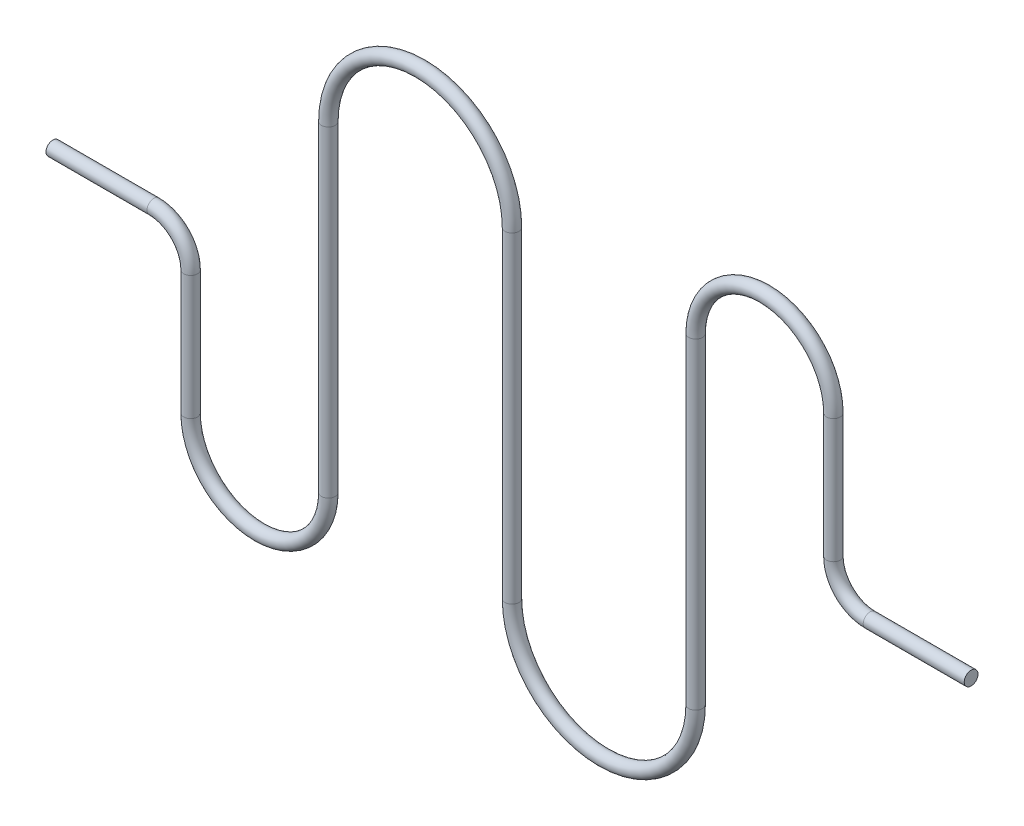
SolidWorks part; units mm, degrees
material "1060 Alloy"
ref_plane "Front Plane" through (0, 0, 0) normal (0, 0, 1) x (1, 0, 0)
ref_plane "Top Plane" through (0, 0, 0) normal (0, 1, 0) x (1, 0, 0)
ref_plane "Right Plane" through (0, 0, 0) normal (1, 0, 0) x (0, 0, -1)
sketch "Sketch4" plane through (0, 0, 0) normal (0, 0, 1) x (1, 0, 0)
  line L0 (0, -44.45) -> (0, 44.45)
  line L7 (50.8, -44.45) -> (50.8, 44.45)
  line L8 (-50.8, -44.45) -> (-50.8, 44.45)
  line L9 (-88.9, -44.45) -> (-88.9, -10.16)
  line L10 (-99.06, 0) -> (-127, 0)
  line L11 (88.9, 44.45) -> (88.9, 10.16)
  line L12 (99.06, 0) -> (127, 0)
  arc A0 (0, -44.45) -> (50.8, -44.45) centre (25.4, -44.45) ccw
  arc A1 (0, 44.45) -> (-50.8, 44.45) centre (-25.4, 44.45) ccw
  arc A2 (-50.8, -44.45) -> (-88.9, -44.45) centre (-69.85, -44.45) cw
  arc A3 (50.8, 44.45) -> (88.9, 44.45) centre (69.85, 44.45) cw
  arc A4 (-88.9, -10.16) -> (-99.06, 0) centre (-99.06, -10.16) ccw
  arc A5 (99.06, 0) -> (88.9, 10.16) centre (99.06, 10.16) cw
  point P0 (0, 0)
  point P3 (-88.9, 0)
  point P9 (0, 0)
  point P12 (50.8, 0)
  point P15 (-50.8, 0)
  point P27 (88.9, 0)
  dimension "D6" = 10.16
  dimension "D1" = 25.4
  dimension "D2" = 19.05
  dimension "D4" = 51.1953
  dimension "D3" = 38.1
ref_plane "Plane1" through (127, 0, 0) normal (1, 0, 0) x (0, 0, -1)
sketch "Sketch7" plane through (127, 0, 0) normal (1, 0, 0) x (0, 0, -1)
  circle A0 centre (0, 0) radius 1.905
  dimension "D1" = 3.81
sweep "Sweep3" add profiles "Sketch7" path "Sketch4"
